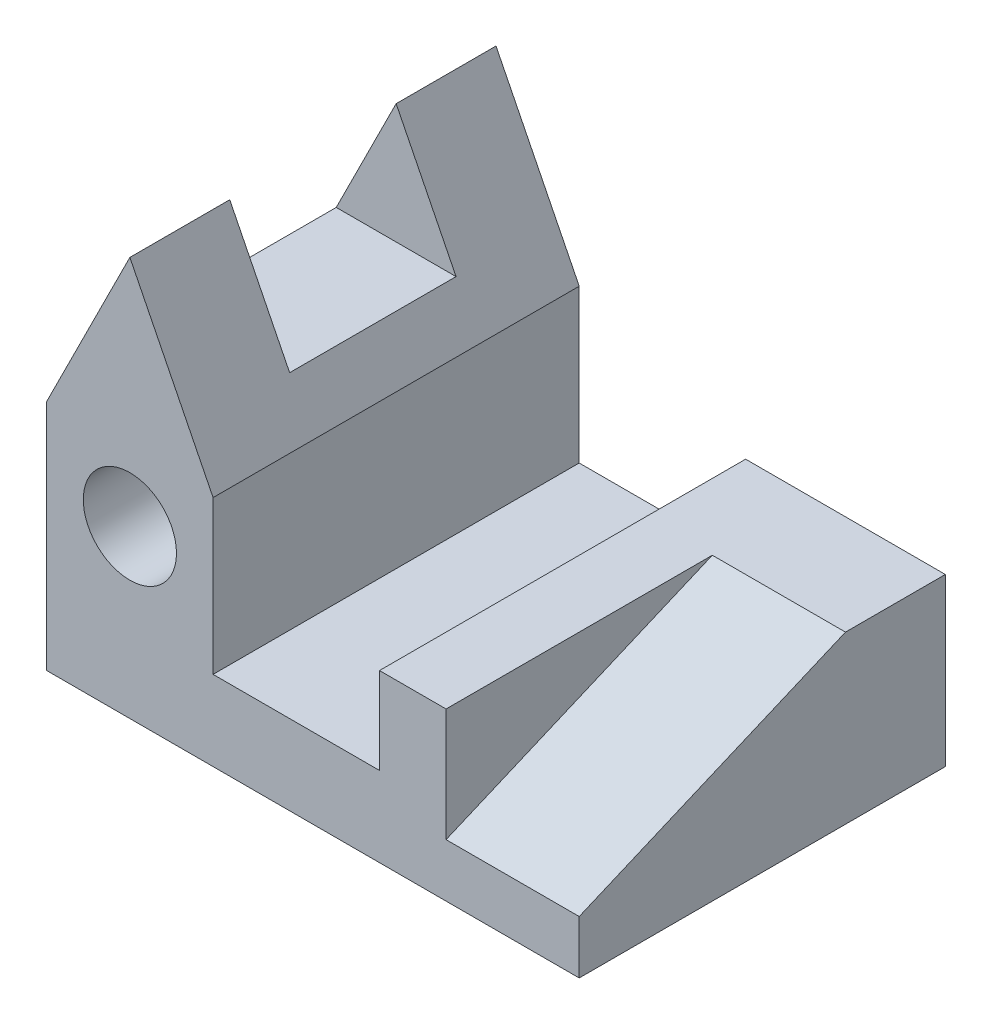
SolidWorks part; units mm, degrees
material "Plain Carbon Steel"
ref_plane "Front Plane" through (0, 0, 0) normal (0, 0, 1) x (1, 0, 0)
ref_plane "Top Plane" through (0, 0, 0) normal (0, 1, 0) x (1, 0, 0)
ref_plane "Right Plane" through (0, 0, 0) normal (1, 0, 0) x (0, 0, -1)
sketch "Sketch7" plane through (0, 0, 0) normal (0, 0, 1) x (1, 0, 0)
  line L1 (0, 0) -> (80, 0)
  line L2 (0, 0) -> (0, 35)
  line L4 (80, 0) -> (80, 25)
  line L5 (25, 12) -> (50, 12)
  line L6 (25, 12) -> (25, 35)
  line L8 (50, 12) -> (50, 25)
  line L11 (80, 25) -> (50, 25)
  line L13 (0, 35) -> (12.5, 60)
  line L14 (12.5, 60) -> (25, 35)
  dimension "D1" = 60
  dimension "D2" = 80
  dimension "D3" = 12
  dimension "D4" = 25
  dimension "D5" = 25
  dimension "D6" = 35
  dimension "D7" = 30
extrude "Boss-Extrude2" add sketch "Sketch7" along normal blind 55
sketch "Sketch8" plane through (0, 0, 55) normal (0, 0, 1) x (1, 0, 0)
  line L0 (0, 25) -> (25, 25) construction
  line L1 (12.5, 75.4796) -> (12.5, 60) construction
  line L2 (12.5, 32) -> (12.5, 18) construction
  circle A0 centre (12.5, 25) radius 7
  dimension "D3" = 14
extrude "Cut-Extrude2" cut sketch "Sketch8" against normal through all
ref_plane "Plane1" through (0, 0, 40) normal (0, 0, 1) x (1, 0, 0)
sketch "Sketch10" plane through (0, 0, 40) normal (0, 0, 1) x (1, 0, 0)
  line L0 (3.5, 42) -> (21.5, 42)
  line L9 (0, 35) -> (0, 0)
  line L10 (0, 0) -> (80, 0)
  line L11 (80, 0) -> (80, 25)
  line L12 (80, 25) -> (50, 25)
  line L13 (50, 25) -> (50, 12)
  line L14 (50, 12) -> (25, 12)
  line L15 (25, 12) -> (25, 35)
  line L16 (25, 35) -> (12.5, 60)
  line L17 (12.5, 60) -> (0, 35)
  line L25 (21.5, 42) -> (12.5, 60)
  line L26 (12.5, 60) -> (3.5, 42)
  dimension "D2" = 18
  dimension "D1" = 0
extrude "Cut-Extrude3" cut sketch "Sketch10" against normal blind 25
sketch "Sketch11" plane through (80, 0, 0) normal (1, 0, 0) x (0, 0, -1)
  line L0 (-15, 25) -> (-55, 8)
  line L1 (-55, 25) -> (0, 25) construction
  line L2 (-55, 0) -> (-55, 25) construction
  line L3 (-55, 8) -> (-55, 25)
  line L4 (-55, 25) -> (-15, 25)
  line L9 (0, 0) -> (0, 25)
  line L10 (0, 25) -> (-55, 25)
  line L11 (-55, 25) -> (-55, 0)
  line L12 (-55, 0) -> (0, 0)
  line L14 (-15, 25) -> (-55, 25)
  line L15 (-55, 25) -> (-55, 8)
  point P10 (0, 0)
  line M9 (0, 25) -> (-55, 25)
  line M10 (-55, 25) -> (-55, 0)
  dimension "D2" = 8
  dimension "D3" = 15
  dimension "D1" = 0
extrude "Cut-Extrude4" cut sketch "Sketch11" against normal blind 20 contours L0 M9 M10
